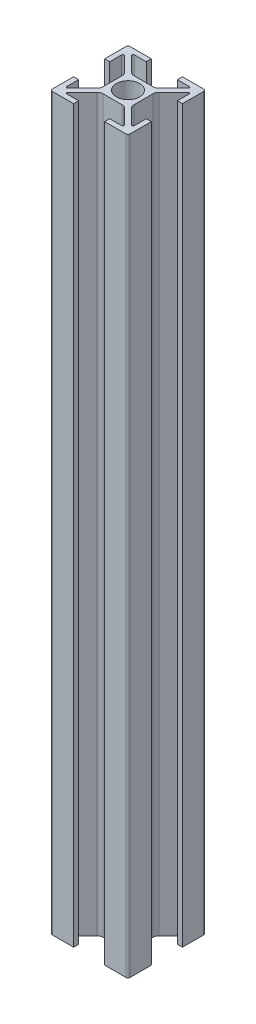
SolidWorks part; units mm, degrees
ref_plane "Plano frontal" through (0, 0, 0) normal (0, 0, 1) x (1, 0, 0)
ref_plane "Plano superior" through (0, 0, 0) normal (0, 1, 0) x (1, 0, 0)
ref_plane "Plano direito" through (0, 0, 0) normal (1, 0, 0) x (0, 0, -1)
sketch "Esboço1" plane through (0, 0, 0) normal (0, 1, 0) x (1, 0, 0)
  line L0 (-7.0565, 8.7) -> (-4, 8.7)
  line L1 (-4, 8.7) -> (-4, 10)
  line L2 (-4, 10) -> (-9.5, 10)
  line L3 (-10, 9.5) -> (-10, 4)
  line L4 (-10, 4) -> (-8.7, 4)
  line L5 (-8.7, 4) -> (-8.7, 7.0565)
  line L6 (-8.1879, 7.2686) -> (-4.4393, 3.5201)
  line L7 (-4, 2.4594) -> (-4, -2.4594)
  line L8 (-4.4393, -3.5201) -> (-8.1879, -7.2686)
  line L9 (-8.7, -7.0565) -> (-8.7, -4)
  line L10 (-8.7, -4) -> (-10, -4)
  line L11 (-10, -4) -> (-10, -9.5)
  line L12 (-9.5, -10) -> (-4, -10)
  line L13 (-4, -10) -> (-4, -8.7)
  line L14 (-4, -8.7) -> (-7.0565, -8.7)
  line L15 (-7.2686, -8.1879) -> (-3.5201, -4.4393)
  line L16 (-2.4594, -4) -> (2.4594, -4)
  line L17 (3.5201, -4.4393) -> (7.2686, -8.1879)
  line L18 (7.0565, -8.7) -> (4, -8.7)
  line L19 (4, -8.7) -> (4, -10)
  line L20 (4, -10) -> (9.5, -10)
  line L21 (10, -9.5) -> (10, -4)
  line L22 (10, -4) -> (8.7, -4)
  line L23 (8.7, -4) -> (8.7, -7.0565)
  line L24 (8.1879, -7.2686) -> (4.4393, -3.5201)
  line L25 (4, -2.4594) -> (4, 2.4594)
  line L26 (4.4393, 3.5201) -> (8.1879, 7.2686)
  line L27 (8.7, 7.0565) -> (8.7, 4)
  line L28 (8.7, 4) -> (10, 4)
  line L29 (10, 4) -> (10, 9.5)
  line L30 (9.5, 10) -> (4, 10)
  line L31 (4, 10) -> (4, 8.7)
  line L32 (4, 8.7) -> (7.0565, 8.7)
  line L33 (7.2686, 8.1879) -> (3.5201, 4.4393)
  line L34 (2.4594, 4) -> (-2.4594, 4)
  line L35 (-3.5201, 4.4393) -> (-7.2686, 8.1879)
  circle A0 centre (0, 0) radius 3
  arc A1 (-7.0565, 8.7) -> (-7.2686, 8.1879) centre (-7.0565, 8.4) ccw
  arc A2 (-9.5, 10) -> (-10, 9.5) centre (-9.5, 9.5) ccw
  arc A3 (-8.1879, 7.2686) -> (-8.7, 7.0565) centre (-8.4, 7.0565) ccw
  arc A4 (-4, 2.4594) -> (-4.4393, 3.5201) centre (-5.5, 2.4594) ccw
  arc A5 (-4.4393, -3.5201) -> (-4, -2.4594) centre (-5.5, -2.4594) ccw
  arc A6 (-8.7, -7.0565) -> (-8.1879, -7.2686) centre (-8.4, -7.0565) ccw
  arc A7 (-10, -9.5) -> (-9.5, -10) centre (-9.5, -9.5) ccw
  arc A8 (-7.2686, -8.1879) -> (-7.0565, -8.7) centre (-7.0565, -8.4) ccw
  arc A9 (-2.4594, -4) -> (-3.5201, -4.4393) centre (-2.4594, -5.5) ccw
  arc A10 (3.5201, -4.4393) -> (2.4594, -4) centre (2.4594, -5.5) ccw
  arc A11 (7.0565, -8.7) -> (7.2686, -8.1879) centre (7.0565, -8.4) ccw
  arc A12 (9.5, -10) -> (10, -9.5) centre (9.5, -9.5) ccw
  arc A13 (8.1879, -7.2686) -> (8.7, -7.0565) centre (8.4, -7.0565) ccw
  arc A14 (4, -2.4594) -> (4.4393, -3.5201) centre (5.5, -2.4594) ccw
  arc A15 (4.4393, 3.5201) -> (4, 2.4594) centre (5.5, 2.4594) ccw
  arc A16 (8.7, 7.0565) -> (8.1879, 7.2686) centre (8.4, 7.0565) ccw
  arc A17 (10, 9.5) -> (9.5, 10) centre (9.5, 9.5) ccw
  arc A18 (7.2686, 8.1879) -> (7.0565, 8.7) centre (7.0565, 8.4) ccw
  arc A19 (2.4594, 4) -> (3.5201, 4.4393) centre (2.4594, 5.5) ccw
  arc A20 (-3.5201, 4.4393) -> (-2.4594, 4) centre (-2.4594, 5.5) ccw
extrude "Ressalto-extrusão1" add sketch "Esboço1" along normal blind 188
